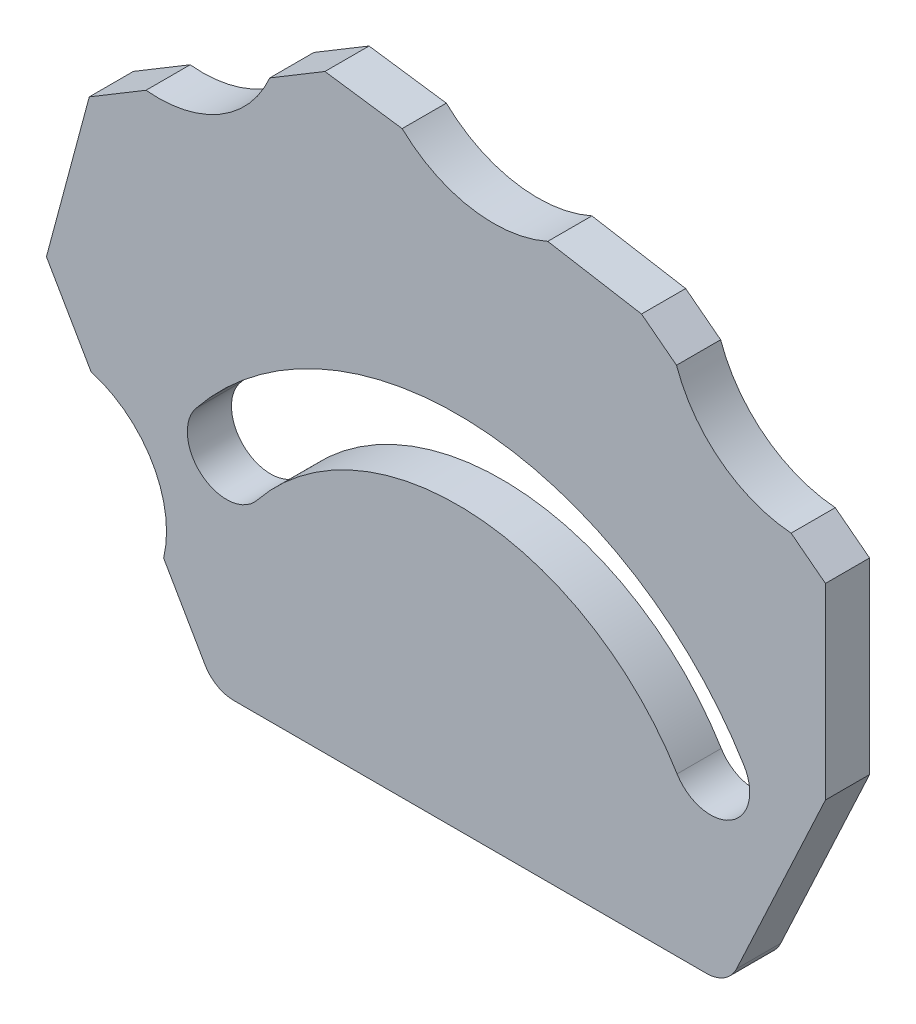
SolidWorks part; units mm, degrees
ref_plane "Front Plane" through (0, 0, 0) normal (0, 0, 1) x (1, 0, 0)
ref_plane "Top Plane" through (0, 0, 0) normal (0, 1, 0) x (1, 0, 0)
ref_plane "Right Plane" through (0, 0, 0) normal (1, 0, 0) x (0, 0, -1)
sketch "Sketch1" plane through (0, 0, 0) normal (0, 0, 1) x (1, 0, 0)
  line L0 (-49.4165, -244.8125) -> (743.9169, -244.8125) construction
  line L1 (38.961, 13.16) -> (42.961, 13.16)
  line L2 (38.961, 13.16) -> (38.961, -13.16)
  line L3 (38.961, -13.16) -> (42.961, -13.16)
  line L4 (42.961, 13.16) -> (42.961, -13.16)
  line L5 (-146.7582, -31.6105) -> (-100.2582, -31.6105)
  line L6 (-22.8189, -33.5966) -> (43.1811, -33.5966)
  line L7 (-22.8189, -33.5966) -> (-22.8189, -46.6075)
  line L8 (-22.8189, -46.6075) -> (43.1811, -46.6075)
  line L9 (43.1811, -33.5966) -> (43.1811, -46.6075)
  line L10 (-91.3984, -12.6105) -> (-100.2582, -31.6105)
  line L11 (-91.3984, -12.6105) -> (-91.3984, 4.3895)
  line L13 (-151.377, -23.6105) -> (-146.7582, -31.6105)
  line L14 (-161.9991, -5.2702) -> (-157.9576, -12.2702)
  line L15 (-161.9991, -5.2702) -> (-158.1168, 9.2187)
  line L16 (-158.1168, 9.2187) -> (-152.9738, 12.309)
  line L17 (-141.7595, 18.8846) -> (-136.7595, 21.889)
  line L18 (-136.7595, 21.889) -> (-129.7595, 20.9052)
  line L19 (-129.7595, 20.9052) -> (-116.5659, 18.6523) construction
  line L20 (-116.5659, 18.6523) -> (-108.0659, 17.2009)
  line L21 (-108.0659, 17.2009) -> (-104.8972, 14.7653)
  line L22 (-104.8972, 14.7653) -> (-94.5095, 6.7808) construction
  line L23 (-94.5095, 6.7808) -> (-91.3984, 4.3895)
  arc A0 (-157.9576, -12.2702) -> (-151.377, -23.6105) centre (-160.6145, -21.3914) cw
  arc A1 (-152.9738, 12.309) -> (-141.7595, 18.8846) centre (-151.8554, 23.2519) ccw
  arc A2 (-129.7595, 20.9052) -> (-116.5659, 18.6523) centre (-121.4795, 29.6361) ccw
  arc A3 (-104.8972, 14.7653) -> (-94.5095, 6.7808) centre (-93.5761, 18.7445) ccw
  arc A4 (-145.6766, -12.61) -> (-101.8098, -15.4352) centre (-124.7332, -29.3939) cw construction
  arc A5 (-98.776, -13.5879) -> (-148.4484, -10.3888) centre (-124.7332, -29.3939) ccw
  arc A6 (-104.8437, -17.2826) -> (-142.9048, -14.8313) centre (-124.7332, -29.3939) ccw
  arc A7 (-104.8437, -17.2826) -> (-98.776, -13.5879) centre (-101.8098, -15.4352) ccw
  arc A8 (-148.4484, -10.3888) -> (-142.9048, -14.8313) centre (-145.6766, -12.61) ccw
  point P14 (-104.8972, 14.7653)
  point P27 (-123.1627, 19.7787)
  point P28 (-94.5095, 6.7808)
  point P36 (-123.0082, -2.6105)
  point P41 (-123.5082, -31.6105)
  dimension "D10" = 9.5003
  dimension "D15" = 11
  dimension "D20" = 8.804
  dimension "D27" = 12
  dimension "D1" = 4
  dimension "D2" = 66
  dimension "D3" = 115
  dimension "D4" = 46.5
  dimension "D5" = 19
  dimension "D6" = 17
  dimension "D7" = 3.1686
  dimension "D8" = 3.1111
  dimension "D9" = 8
  dimension "D11" = 2.2192
  dimension "D12" = 7
  dimension "D13" = 15
  dimension "D14" = 6
  dimension "D16" = 120
  dimension "D17" = 135
  dimension "D18" = 136
  dimension "D19" = 13
  dimension "D21" = 5
  dimension "D22" = 7
  dimension "D23" = 141
  dimension "D24" = 10
  dimension "D25" = 8.5
  dimension "D26" = 152.142
  dimension "D28" = 29
  dimension "D29" = 0.5
extrude "Boss-Extrude1" add sketch "Sketch1" along normal blind 4 contours A3 L23 L11 L10 L5 L13 A0 L14 L15 L16 A1 L17 L18 A2 L20 L21 | A6 A8 A5 A7
fillet "Fillet1" radius 3 2 edges at (-146.7582, -31.6105, 2) (-100.2582, -31.6105, 2)
